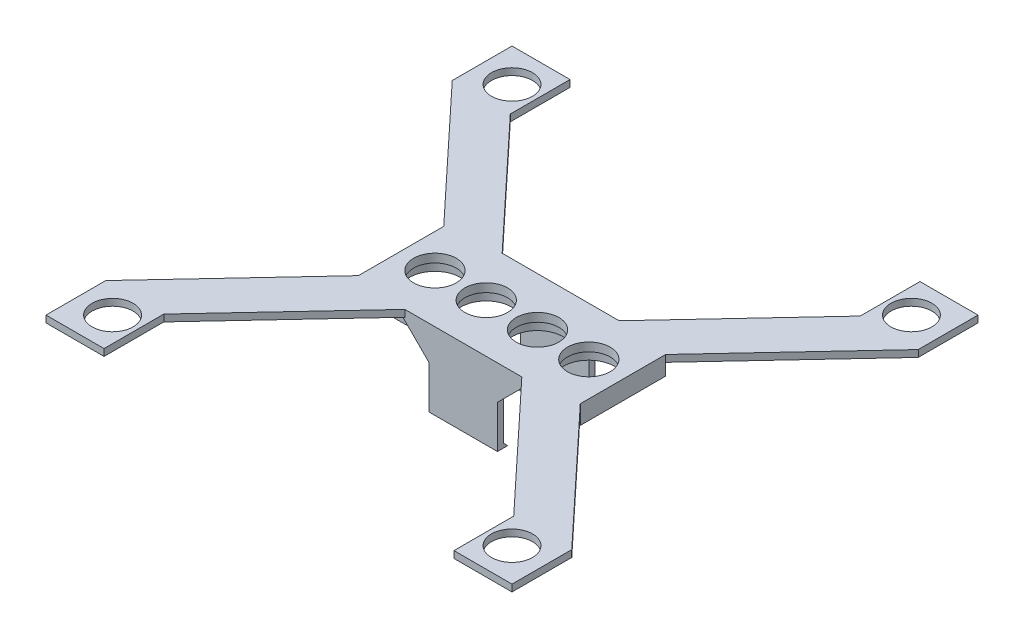
SolidWorks part; units mm, degrees
ref_plane "Přední rovina" through (0, 0, 0) normal (0, 0, 1) x (1, 0, 0)
ref_plane "Horní rovina" through (0, 0, 0) normal (0, 1, 0) x (1, 0, 0)
ref_plane "Pravá rovina" through (0, 0, 0) normal (1, 0, 0) x (0, 0, -1)
sketch "Skica1" plane through (0, 0, 0) normal (0, 0, 1) x (1, 0, 0)
  line L0 (-52.1567, -7.7147) -> (-26.1567, -7.7147)
  line L12 (-52.1567, -6.7147) -> (-26.1567, -6.7147)
  line L15 (-52.1567, -6.7147) -> (-52.1567, -7.7147)
  line L18 (-26.1567, -6.7147) -> (-26.1567, -7.7147)
  point P2 (-39.1567, -7.7147)
  dimension "D1" = 13
  dimension "D2" = 1
extrude "Přidat vysunutím1" add sketch "Skica1" along normal blind 10 contours L0 L18 L12 L15
sketch "Skica2" plane through (0, -7.7147, 0) normal (0, -1, 0) x (-1, 0, 0)
  line L0 (26.1567, -10) -> (26.1567, 0) construction
  line L1 (52.1567, -10) -> (26.1567, -10) construction
  circle A0 centre (48.1867, -5) radius 2.5
  circle A1 centre (42.1767, -5) radius 2.5
  circle A2 centre (36.1667, -5) radius 2.5
  circle A3 centre (30.1567, -5) radius 2.5
  dimension "D1" = 5
  dimension "D3" = 5
  dimension "D5" = 4
  dimension "D4" = 4
extrude "Odebrat vysunutím1" cut sketch "Skica2" against normal blind 1
sketch "Skica3" plane through (0, -6.7147, 0) normal (0, 1, 0) x (1, 0, 0)
  line L0 (-32.9567, 0) -> (-18.6567, 15.3)
  line L25 (-52.1567, 0) -> (-26.1567, 0) construction
  line L27 (-26.1567, 0) -> (-11.8567, 15.3)
  line L29 (-26.1567, 0) -> (-32.9567, 0)
  line L34 (-52.1567, 0) -> (-45.3567, 0)
  line L35 (-52.1567, 0) -> (-66.4567, 15.3)
  line L37 (-45.3567, 0) -> (-59.6567, 15.3)
  line L47 (-45.3567, -10) -> (-59.6567, -25.3)
  line L49 (-52.1567, -10) -> (-66.4567, -25.3)
  line L50 (-52.1567, -10) -> (-45.3567, -10)
  line L51 (-26.1567, -10) -> (-32.9567, -10)
  line L53 (-26.1567, -10) -> (-11.8567, -25.3)
  line L54 (-32.9567, -10) -> (-18.6567, -25.3)
  line L55 (-52.1567, -10) -> (-26.1567, -10) construction
  line L56 (-66.4567, 15.3) -> (-66.4567, 22.3)
  line L57 (-66.4567, 22.3) -> (-59.6567, 22.3)
  line L59 (-59.6567, 22.3) -> (-59.6567, 15.3)
  line L60 (-59.6567, -25.3) -> (-59.6567, -32.3)
  line L61 (-59.6567, -32.3) -> (-66.4567, -32.3)
  line L62 (-66.4567, -32.3) -> (-66.4567, -25.3)
  line L63 (-18.6567, -25.3) -> (-18.6567, -32.3)
  line L64 (-18.6567, -32.3) -> (-11.8567, -32.3)
  line L65 (-11.8567, -32.3) -> (-11.8567, -25.3)
  line L66 (-11.8567, 15.3) -> (-11.8567, 22.3)
  line L67 (-11.8567, 22.3) -> (-18.6567, 22.3)
  line L68 (-18.6567, 22.3) -> (-18.6567, 15.3)
  circle A0 centre (-62.5567, 18.4) radius 2.4
  circle A1 centre (-15.7567, 18.4) radius 2.4
  circle A2 centre (-62.5567, -28.4) radius 2.4
  circle A3 centre (-15.7567, -28.4) radius 2.4
  point P18 (0, 0)
  dimension "D7" = 6.8
  dimension "D9" = 4.8
  dimension "D14" = 4.8
  dimension "D18" = 4.8
  dimension "D31" = 4.8
  dimension "D3" = 7
  dimension "D10" = 6.8
  dimension "D11" = 0
  dimension "D12" = 3.9
  dimension "D13" = 3.9
  dimension "D15" = 7
  dimension "D16" = 0
  dimension "D17" = 3.9
  dimension "D19" = 3.9
  dimension "D20" = 3.9
  dimension "D21" = 6.8
  dimension "D22" = 6.8
  dimension "D23" = 6.8
  dimension "D24" = 0
  dimension "D25" = 6.8
  dimension "D26" = 54.6
  dimension "D27" = 54.6
  dimension "D28" = 6.8
  dimension "D29" = 54.6
  dimension "D30" = 54.6
  dimension "D32" = 3.9
  dimension "D33" = 6.8
  dimension "D34" = 3.9
  dimension "D35" = 3.9
  dimension "D36" = 22.3
  dimension "D37" = 22.3
  dimension "D38" = 10
  dimension "D39" = 10
extrude "Přidat vysunutím2" add sketch "Skica3" against normal blind 0.8
sketch "Skica4" plane through (0, -7.7147, 0) normal (0, -1, 0) x (-1, 0, 0)
  line L1 (52.1567, -10) -> (26.1567, -10)
  line L2 (52.1567, -10) -> (52.1567, 0)
  line L3 (52.1567, 0) -> (26.1567, 0)
  line L4 (26.1567, -10) -> (26.1567, 0)
  circle A0 centre (48.1867, -5) radius 3
  circle A1 centre (42.1767, -5) radius 3
  circle A2 centre (36.1667, -5) radius 3
  circle A3 centre (30.1567, -5) radius 3
  point P18 (0, 0)
  point P19 (0, 0)
  point P20 (0, 0)
  dimension "D1" = 6
  dimension "D2" = 6
  dimension "D3" = 6
  dimension "D4" = 6
extrude "Přidat vysunutím3" add sketch "Skica4" along normal blind 1.2
sketch "Skica6" plane through (0, -6.7147, 0) normal (0, 1, 0) x (1, 0, 0)
  line L0 (-45.3567, 0) -> (-32.9567, 0) construction
  line L1 (-43.1567, 0) -> (-35.1567, 0)
  line L2 (-43.1567, 0) -> (-43.1567, 0.7)
  line L3 (-43.1567, 0.7) -> (-35.1567, 0.7)
  line L4 (-35.1567, 0) -> (-35.1567, 0.7)
  line L5 (-45.3567, -10) -> (-32.9567, -10) construction
  line L6 (-43.1567, -10) -> (-35.1567, -10)
  line L7 (-43.1567, -10) -> (-43.1567, -10.7)
  line L8 (-43.1567, -10.7) -> (-35.1567, -10.7)
  line L9 (-35.1567, -10) -> (-35.1567, -10.7)
  dimension "D1" = 0.7
  dimension "D2" = 8
  dimension "D3" = 2.2
  dimension "D4" = 2.2
  dimension "D5" = 0.7
extrude "Přidat vysunutím5" add sketch "Skica6" against normal blind 9
sketch "Skica7" plane through (-35.1567, 0, 0) normal (1, 0, 0) x (0, 0, -1)
  line L9 (-10, -15.7147) -> (-9.5, -15.7147)
  line L10 (-9.5, -15.7147) -> (-10, -15.2147)
  line L11 (-10, -15.7147) -> (-10, -8.9147) construction
  line L12 (-10, -15.2147) -> (-10, -15.7147)
  line L13 (0, -15.7147) -> (0, -15.2147)
  line L14 (0, -15.7147) -> (0, -8.9147) construction
  line L15 (0, -15.2147) -> (-0.5, -15.7147)
  line L16 (-0.5, -15.7147) -> (0, -15.7147)
  dimension "D1" = 0.5
  dimension "D2" = 0.5
  dimension "D3" = 0.5
extrude "Přidat vysunutím6" add sketch "Skica7" against normal blind 8
sketch "Skica8" plane through (0, 0, 0) normal (0, 0, -1) x (-1, 0, 0)
  line L0 (43.1567, -6.7147) -> (43.1567, -10.7147)
  line L1 (43.1567, -15.2147) -> (43.1567, -8.9147) construction
  line L2 (43.1567, -6.7147) -> (47.1567, -6.7147)
  line L3 (47.1567, -6.7147) -> (43.1567, -10.7147)
  line L4 (35.1567, -10.7147) -> (35.1567, -6.7147)
  line L5 (35.1567, -15.2147) -> (35.1567, -8.9147) construction
  line L6 (35.1567, -6.7147) -> (31.1567, -6.7147)
  line L7 (31.1567, -6.7147) -> (35.1567, -10.7147)
  dimension "D1" = 4
  dimension "D2" = 4
  dimension "D3" = 4
extrude "Přidat vysunutím8" add sketch "Skica8" along normal blind 0.7
sketch "Skica9" plane through (0, 0, 10) normal (0, 0, 1) x (1, 0, 0)
  line L0 (-43.1567, -6.7147) -> (-47.1567, -6.7147)
  line L1 (-59.6567, -6.7147) -> (-45.3567, -6.7147) construction
  line L2 (-43.1567, -6.7147) -> (-43.1567, -10.7147)
  line L3 (-43.1567, -15.7147) -> (-43.1567, -6.7147) construction
  line L4 (-43.1567, -10.7147) -> (-47.1567, -6.7147)
  line L5 (-35.1567, -6.7147) -> (-35.1567, -10.7147)
  line L6 (-35.1567, -15.2147) -> (-35.1567, -8.9147) construction
  line L7 (-35.1567, -10.7147) -> (-31.1567, -6.7147)
  line L8 (-31.1567, -6.7147) -> (-35.1567, -6.7147)
  dimension "D1" = 4
  dimension "D2" = 4
extrude "Přidat vysunutím9" add sketch "Skica9" along normal blind 0.7
